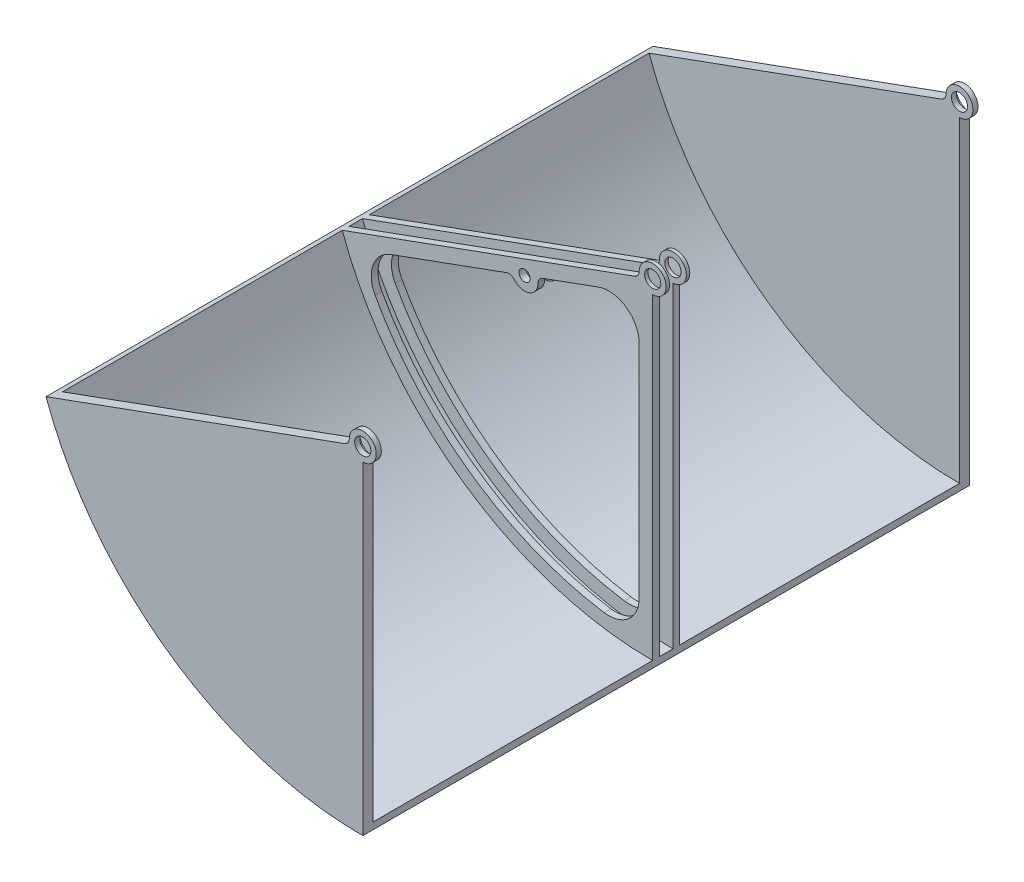
SolidWorks part; units mm, degrees
ref_plane "Płaszczyzna przednia" through (0, 0, 0) normal (0, 0, 1) x (1, 0, 0)
ref_plane "Płaszczyzna górna" through (0, 0, 0) normal (0, 1, 0) x (1, 0, 0)
ref_plane "Płaszczyzna prawa" through (0, 0, 0) normal (1, 0, 0) x (0, 0, -1)
sketch "Szkic1" plane through (0, 0, 0) normal (0, 0, 1) x (1, 0, 0)
  line L0 (-469.8463, -171.0101) -> (0, 0)
  line L1 (0, 0) -> (0, -500)
  arc A0 (0, -500) -> (-469.8463, -171.0101) centre (0, 0) cw
  dimension "D1" = 500
  dimension "D2" = 70
extrude "Dodanie-wyciągnięcie1" add sketch "Szkic1" along normal blind 900
shell "Skorupa1" thickness 10
sketch "Szkic4" plane through (0, 0, 0) normal (0, 0, -1) x (-1, 0, 0)
  line L1 (0, -20) -> (0, -490)
  line L2 (460.4494, -167.5899) -> (18.7939, -6.8404)
  arc A0 (460.4494, -167.5899) -> (0, -490) centre (0, 0) cw
  arc A1 (0, -20) -> (18.7939, -6.8404) centre (0, 0) cw
  circle A2 centre (0, 0) radius 12
  dimension "D1" = 20
  dimension "D2" = 24
extrude "Dodanie-wyciągnięcie3" add sketch "Szkic4" against normal blind 15
ref_plane "Płaszczyzna1" through (0, 0, 450) normal (0, 0, 1) x (1, 0, 0)
mirror "Lustro1" about plane through (0, 0, 450) normal (0, 0, 1) of "Dodanie-wyciągnięcie3"
ref_plane "Płaszczyzna2" through (0, 0, 440) normal (0, 0, 1) x (1, 0, 0)
sketch "Szkic6" plane through (0, 0, 440) normal (0, 0, 1) x (1, 0, 0)
  line L0 (-18.7939, -6.8404) -> (-460.4494, -167.5899)
  line L1 (0, -500) -> (0, -20) construction
  line L2 (0, -20) -> (0, -490)
  line L3 (-20, -28.563) -> (-20, -469.5743)
  line L4 (-20, -28.563) -> (-171.3011, -83.6321)
  line L5 (-208.8888, -97.3129) -> (-434.4151, -179.3977)
  line L6 (-20, -28.563) -> (-434.4151, -179.3977) construction
  arc A0 (-460.4494, -167.5899) -> (0, -490) centre (0, 0) ccw
  arc A1 (0, -20) -> (-18.7939, -6.8404) centre (0, 0) ccw
  circle A2 centre (0, 0) radius 12
  arc A3 (-434.4151, -179.3977) -> (-20, -469.5743) centre (0, 0) ccw
  arc A4 (-20, -28.563) -> (-20, -28.563) centre (-20, -28.563) ccw
  circle A5 centre (-190.095, -90.4725) radius 8.15
  arc A6 (-208.8888, -97.3129) -> (-171.3011, -83.6321) centre (-190.095, -90.4725) ccw
  dimension "D1" = 490
  dimension "D4" = 24
  dimension "D7" = 260
  dimension "D8" = 16.3
  dimension "D9" = 20
  dimension "D2" = 20
  dimension "D5" = 20
  dimension "D6" = 70
  dimension "D10" = 470
extrude "Dodanie-wyciągnięcie4" add sketch "Szkic6" against normal blind 10
mirror "Lustro6" about plane through (0, 0, 450) normal (0, 0, 1) of "Dodanie-wyciągnięcie4"
fillet "Zaokrąglenie3" radius 45 6 edges at (-20, -28.563, 435) (-20, -469.5743, 465) (-20, -469.5743, 435) (-20, -28.563, 465) (-434.4151, -179.3977, 465) (-434.4151, -179.3977, 435)
sketch "Szkic8" plane through (0, 0, 0) normal (0, 0, -1) x (-1, 0, 0)
  circle A0 centre (0, 0) radius 20
extrude "Wytnij-wyciągnięcie1" cut sketch "Szkic8" against normal blind 7.5
sketch "Szkic11" plane through (0, 0, 430) normal (0, 0, -1) x (-1, 0, 0)
  circle A1 centre (0, 0) radius 20
extrude "Wytnij-wyciągnięcie2" cut sketch "Szkic11" against normal blind 5
sketch "Szkic12" plane through (0, 0, 460) normal (0, 0, -1) x (-1, 0, 0)
  circle A0 centre (0, 0) radius 20
extrude "Wytnij-wyciągnięcie3" cut sketch "Szkic12" against normal blind 5
sketch "Szkic13" plane through (0, 0, 885) normal (0, 0, -1) x (-1, 0, 0)
  circle A0 centre (0, 0) radius 20
extrude "Wytnij-wyciągnięcie4" cut sketch "Szkic13" against normal blind 7.5
fillet "Zaokrąglenie4" radius 10 4 edges at (-18.7939, -6.8404, 11.25) (-18.7939, -6.8404, 437.5) (-18.7939, -6.8404, 467.5) (-18.7939, -6.8404, 896.25)
fillet "Zaokrąglenie5" radius 10 4 edges at (-208.8888, -97.3129, 435) (-208.8888, -97.3129, 465) (-171.3011, -83.6321, 435) (-171.3011, -83.6321, 465)
